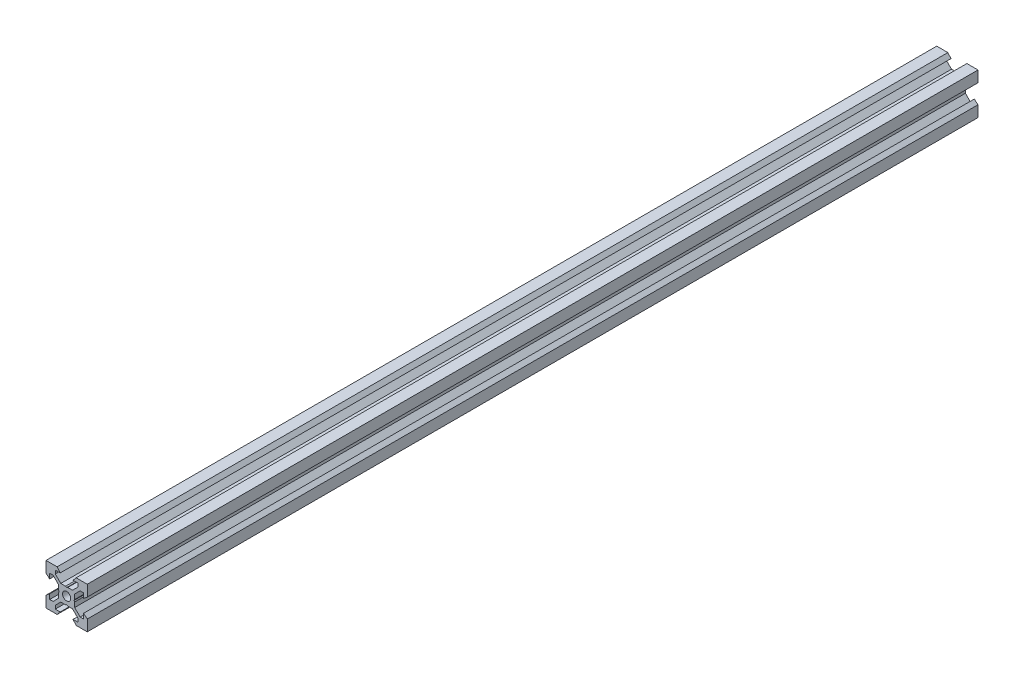
SolidWorks part; units mm, degrees
ref_plane "Front Plane" through (0, 0, 0) normal (0, 0, 1) x (1, 0, 0)
ref_plane "Top Plane" through (0, 0, 0) normal (0, 1, 0) x (1, 0, 0)
ref_plane "Right Plane" through (0, 0, 0) normal (1, 0, 0) x (0, 0, -1)
sketch "Sketch1" plane through (0, 0, 0) normal (0, 0, 1) x (1, 0, 0)
  line L0 (10, 10) -> (4.6104, 10) construction
  line L1 (10, 10) -> (10, 4.6104) construction
  line L2 (10, -10) -> (10, -4.6104) construction
  line L3 (10, -10) -> (4.6104, -10) construction
  line L4 (10, 10) -> (10, 4.6104)
  line L5 (6.5607, 5.5) -> (8.2, 5.5)
  line L6 (5.5, 8.2) -> (5.5, 6.5607)
  line L7 (10, 10) -> (4.6104, 10)
  line L8 (10, 10) -> (10, 4.6104)
  line L9 (6.5607, 5.5) -> (3.9, 2.8393)
  line L10 (5.5, 6.5607) -> (2.8393, 3.9)
  line L11 (10, 4.6104) -> (8.2, 3.1)
  line L12 (4.6104, 10) -> (3.1, 8.2)
  line L13 (8.2, 3.1) -> (8.2, 5.5)
  line L14 (3.1, 8.2) -> (5.5, 8.2)
  line L15 (-6.5607, 5.5) -> (-8.2, 5.5)
  line L16 (6.5607, -5.5) -> (8.2, -5.5)
  line L17 (3.1, -8.2) -> (5.5, -8.2)
  line L18 (8.2, -3.1) -> (8.2, -5.5)
  line L19 (4.6104, -10) -> (3.1, -8.2)
  line L20 (10, -4.6104) -> (8.2, -3.1)
  line L21 (0.5196, -3.9) -> (0, -3.6)
  line L22 (0.5196, 3.9) -> (0, 3.6)
  line L23 (3.6, 0) -> (3.9, -0.5196)
  line L24 (3.9, 0.5196) -> (3.6, 0)
  line L25 (3.9, 0.5196) -> (3.9, 2.8393)
  line L26 (2.8393, 3.9) -> (0.5196, 3.9)
  line L27 (3.9, -2.8393) -> (3.9, -0.5196)
  line L28 (2.8393, -3.9) -> (0.5196, -3.9)
  line L29 (5.5, -6.5607) -> (2.8393, -3.9)
  line L30 (6.5607, -5.5) -> (3.9, -2.8393)
  line L31 (10, -10) -> (10, -4.6104)
  line L32 (10, -10) -> (4.6104, -10)
  line L33 (5.5, -8.2) -> (5.5, -6.5607)
  line L34 (-6.5607, -5.5) -> (-8.2, -5.5)
  line L35 (10, -10) -> (10, -4.6104)
  line L36 (0, 0) -> (0, 8.2) construction
  line L37 (-10, -10) -> (-4.6104, -10) construction
  line L38 (-10, -10) -> (-10, -4.6104) construction
  line L39 (-10, 10) -> (-10, 4.6104) construction
  line L40 (-10, 10) -> (-4.6104, 10) construction
  line L41 (-10, -10) -> (-10, -4.6104)
  line L43 (-5.5, -8.2) -> (-5.5, -6.5607)
  line L44 (-10, -10) -> (-4.6104, -10)
  line L45 (-10, -10) -> (-10, -4.6104)
  line L46 (-6.5607, -5.5) -> (-3.9, -2.8393)
  line L47 (-5.5, -6.5607) -> (-2.8393, -3.9)
  line L48 (-2.8393, -3.9) -> (-0.5196, -3.9)
  line L49 (-3.9, -2.8393) -> (-3.9, -0.5196)
  line L50 (-2.8393, 3.9) -> (-0.5196, 3.9)
  line L51 (-3.9, 0.5196) -> (-3.9, 2.8393)
  line L52 (-3.9, 0.5196) -> (-3.6, 0)
  line L53 (-3.6, 0) -> (-3.9, -0.5196)
  line L54 (-0.5196, 3.9) -> (0, 3.6)
  line L55 (-0.5196, -3.9) -> (0, -3.6)
  line L56 (-10, -4.6104) -> (-8.2, -3.1)
  line L57 (-4.6104, -10) -> (-3.1, -8.2)
  line L58 (-8.2, -3.1) -> (-8.2, -5.5)
  line L59 (-3.1, -8.2) -> (-5.5, -8.2)
  line L60 (-10, -10) -> (10, -10) construction
  line L61 (-10, -10) -> (-10, 10) construction
  line L62 (-3.1, 8.2) -> (-5.5, 8.2)
  line L63 (-8.2, 3.1) -> (-8.2, 5.5)
  line L64 (-4.6104, 10) -> (-3.1, 8.2)
  line L65 (-10, 4.6104) -> (-8.2, 3.1)
  line L66 (-5.5, 6.5607) -> (-2.8393, 3.9)
  line L67 (-6.5607, 5.5) -> (-3.9, 2.8393)
  line L68 (-10, 10) -> (-10, 4.6104)
  line L69 (-10, 10) -> (-4.6104, 10)
  line L70 (-5.5, 8.2) -> (-5.5, 6.5607)
  line L71 (-10, 10) -> (10, 10) construction
  line L72 (-10, 10) -> (-10, 4.6104)
  line L73 (10, -10) -> (10, 10) construction
  line L74 (-10, -10) -> (10, 10) construction
  line L75 (-10, 10) -> (10, -10) construction
  circle A0 centre (0, 0) radius 2
  dimension "D7" = 4
  dimension "D1" = 20
  dimension "D2" = 5.3896
  dimension "D3" = 4.5
  dimension "D4" = 50
  dimension "D5" = 1.8
  dimension "D6" = 1.5104
  dimension "D8" = 5.5
  dimension "D9" = 120
  dimension "D10" = 0.3
  dimension "D11" = 2.3197
  dimension "D12" = 7.8
  dimension "D13" = 7.8
  dimension "D14" = 1.5
  dimension "D15" = 2.6607
extrude "Boss-Extrude1" add sketch "Sketch1" along normal mid plane 431.74 contours L70 L62 L64 L69 L68 L65 L63 L15 L67 L51 L52 L53 L49 L46 L34 L58 L56 L41 L44 L57 L59 L43 L47 L48 L55 L21 L28 L29 L33 L17 L19 L32 L31 L20 L18 L16 L30 L27 L23 L24 L25 L9 L5 L13 L11 L4 L7 L12 L14 L6 L10
